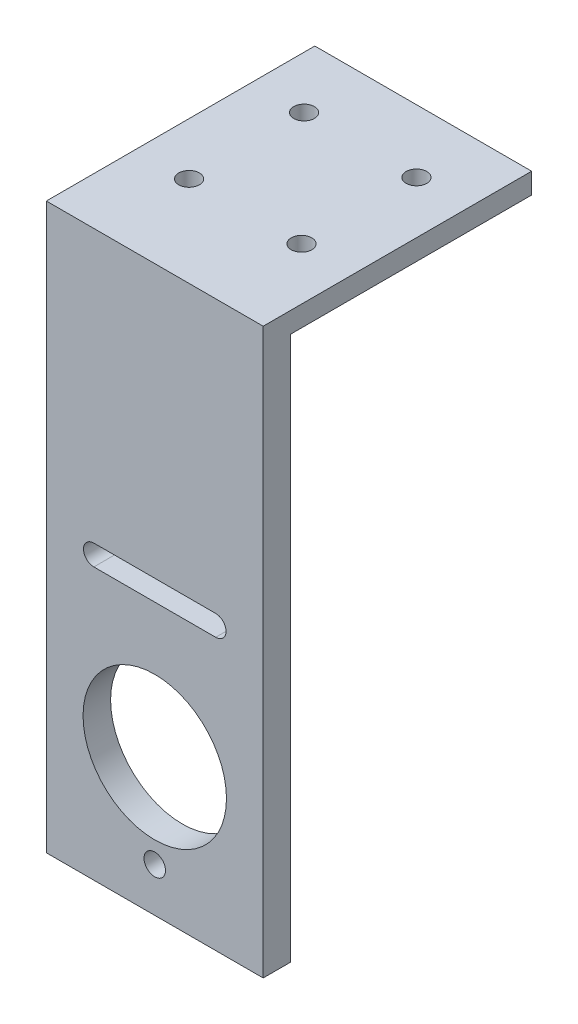
SolidWorks part; units mm, degrees
ref_plane "前视基准面" through (0, 0, 0) normal (0, 0, 1) x (1, 0, 0)
ref_plane "上视基准面" through (0, 0, 0) normal (0, 1, 0) x (1, 0, 0)
ref_plane "右视基准面" through (0, 0, 0) normal (1, 0, 0) x (0, 0, -1)
sketch "草图1" plane through (0, 0, 0) normal (0, 0, 1) x (1, 0, 0)
  line L10 (8.85, 15.7917) -> (-8.85, 15.7917)
  line L11 (8.85, 12.7917) -> (-8.85, 12.7917)
  line L12 (-15.7504, 55.3771) -> (-15.7504, -26.6229)
  line L13 (15.7504, 55.3771) -> (-15.7504, 55.3771)
  line L14 (15.7504, 55.3771) -> (15.7504, -26.6229)
  line L15 (15.7504, -26.6229) -> (-15.7504, -26.6229)
  circle A4 centre (0, -6.7083) radius 10.4175
  arc A5 (-8.85, 15.7917) -> (-8.85, 12.7917) centre (-8.85, 14.2917) ccw
  arc A6 (8.85, 12.7917) -> (8.85, 15.7917) centre (8.85, 14.2917) ccw
  circle A8 centre (0, -20.2083) radius 1.56
  dimension "D1" = 3.12
  dimension "D2" = 82
extrude "凸台-拉伸1" add sketch "草图1" along normal blind 4
sketch "草图3" plane through (0, 0, 0) normal (0, 0, -1) x (-1, 0, 0)
  line L0 (0, 55.3771) -> (0, -24.925) construction
  line L1 (-15.7504, 55.3771) -> (15.7504, 55.3771) construction
  line L2 (-15.7504, 55.3771) -> (-15.7504, -26.6229) construction
  line L3 (-15.7504, 52.3771) -> (15.7504, 52.3771)
  line L4 (-15.7504, 52.3771) -> (-15.7504, 55.3771)
  line L5 (-15.7504, 55.3771) -> (15.7504, 55.3771)
  line L6 (15.7504, 52.3771) -> (15.7504, 55.3771)
  line L7 (15.7504, 55.3771) -> (15.7504, -26.6229) construction
  dimension "D1" = 3
sketch "草图4" plane through (0, 0, 0) normal (0, 0, -1) x (-1, 0, 0)
  line L0 (-15.7504, 55.3771) -> (-15.7504, -26.6229) construction
  line L1 (-15.7504, -23.5462) -> (15.7504, -23.5462)
  line L2 (-15.7504, -23.5462) -> (-15.7504, -27.6335)
  line L3 (-15.7504, -27.6335) -> (15.7504, -27.6335)
  line L4 (15.7504, -23.5462) -> (15.7504, -27.6335)
sketch "草图5" plane through (0, 0, 0) normal (0, 0, 1) x (1, 0, 0)
  line L0 (15.7504, 55.3771) -> (12.6027, 55.3771)
  line L1 (15.7504, 55.3771) -> (-15.7504, 55.3771) construction
  line L2 (12.6027, 55.3771) -> (12.6027, -26.6229)
  line L3 (15.7504, -26.6229) -> (-15.7504, -26.6229) construction
  line L4 (12.6027, -26.6229) -> (15.7504, -26.6229)
  line L5 (15.7504, -26.6229) -> (15.7504, 55.3771)
extrude "凸台-拉伸2" add sketch "草图3" along normal blind 35
sketch "草图6" plane through (0, 52.3771, 0) normal (0, -1, 0) x (1, 0, 0)
  line L0 (-15.7504, -17.5) -> (15.7504, -17.5) construction
  line L1 (-15.7504, -35) -> (-15.7504, 0) construction
  line L2 (15.7504, -35) -> (15.7504, 0) construction
  line L3 (0, 0) -> (0, -35) construction
  line L4 (15.7504, -35) -> (-15.7504, -35) construction
  circle A0 centre (-8.1664, -9.1513) radius 1.5
  circle A1 centre (8.1664, -9.1513) radius 1.5
  circle A2 centre (8.1664, -25.8487) radius 1.5
  circle A3 centre (-8.1664, -25.8487) radius 1.5
  dimension "D1" = 3
extrude "切除-拉伸1" cut sketch "草图6" against normal through all
